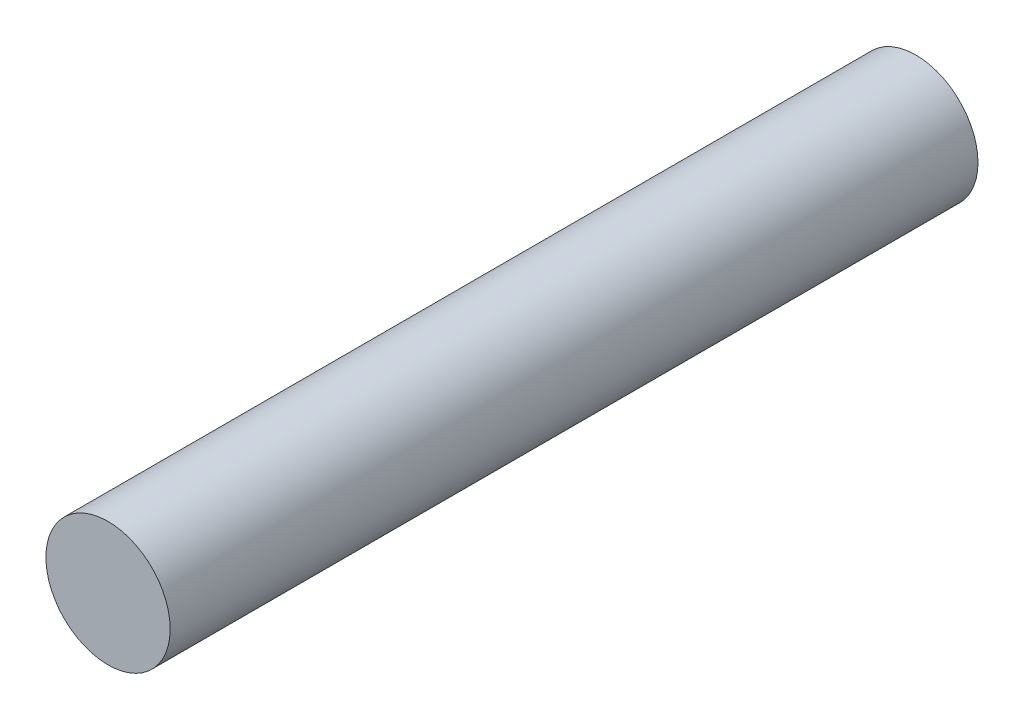
SolidWorks part; units mm, degrees
material "Alloy Steel"
ref_plane "Front Plane" through (0, 0, 0) normal (1, 0, 0) x (0, 1, 0)
ref_plane "Top Plane" through (0, 0, 0) normal (0, 0, 1) x (0, 1, 0)
ref_plane "Right Plane" through (0, 0, 0) normal (0, 1, 0) x (-1, 0, 0)
sketch "Sketch1" plane through (0, 0, 0) normal (0, 0, 1) x (0, 1, 0)
  circle A0 centre (0, 0) radius 4
  dimension "D1" = 8
extrude "Boss-Extrude1" add sketch "Sketch1" along normal blind 26
mirror "Mirror1" about plane through (0, 0, 0) normal (0, 0, 1) of bodies 101
